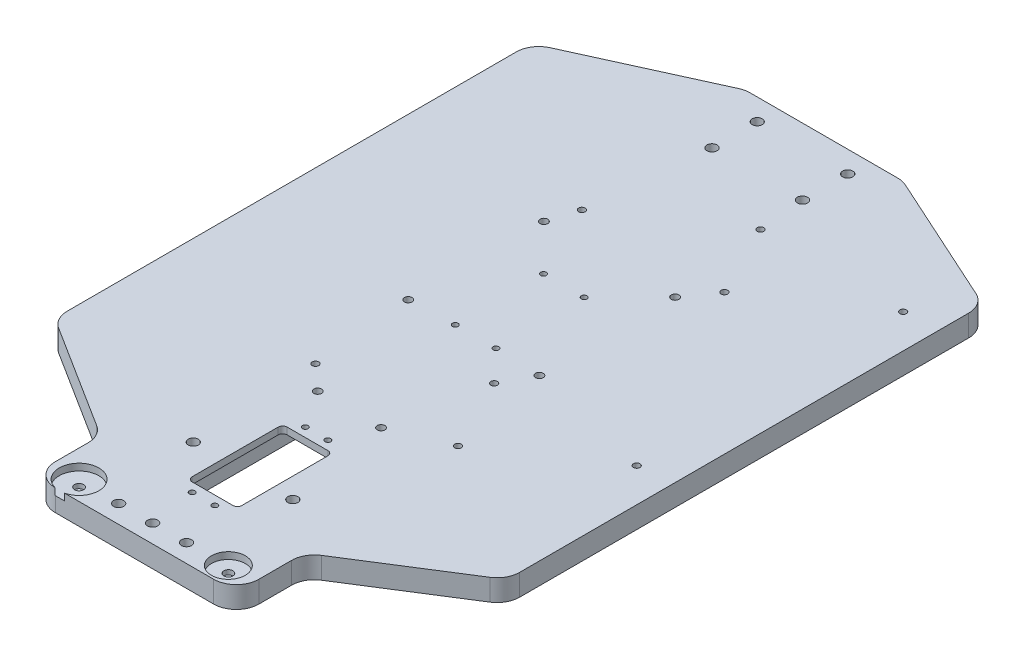
SolidWorks part; units mm, degrees
ref_plane "Front Plane" through (0, 0, 0) normal (0, 0, 1) x (1, 0, 0)
ref_plane "Top Plane" through (0, 0, 0) normal (0, 1, 0) x (1, 0, 0)
ref_plane "Right Plane" through (0, 0, 0) normal (1, 0, 0) x (0, 0, -1)
sketch "Sketch2" plane through (0, 0, 0) normal (0, 1, 0) x (1, 0, 0)
  line L1 (-100, -85.2266) -> (-45, -120)
  line L2 (-45, -120) -> (-45, -150)
  line L3 (-45, -150) -> (0, -150)
  line L4 (0, -150) -> (0, 0)
  line L5 (0, 0) -> (0, 154.8)
  line L6 (0, 154.8) -> (-34.8371, 154.8)
  line L10 (-34.8371, 154.8) -> (-100, 125.1947)
  line L11 (-100, 125.1947) -> (-100, -85.2266)
  dimension "D1" = 304.8
  dimension "D2" = 150
  dimension "D3" = 45
  dimension "D4" = 30
  dimension "D5" = 100
extrude "Chassis Base Shape" add sketch "Sketch2" along normal blind 9.525
hole_wizard "M4 Clearance Hole1" positions "Sketch5" profile "Sketch6" hole size "M4" standard "ANSI Metric" end condition through all
sketch "Sketch5" plane through (0, 0, 0) normal (0, -1, 0) x (-1, 0, 0)
  line L0 (0, -150) -> (0, 154.8) construction
  line L1 (45, -150) -> (0, -150) construction
  point P0 (15, -142)
  point P2 (0, -142)
  point P9 (22, -102)
  dimension "D1" = 15
  dimension "D2" = 8
  dimension "D3" = 22
  dimension "D4" = 40
sketch "Sketch6" plane through (-15, 0, 142) normal (1, 0, 0) x (0, 0, -1)
  line L0 (0, 0) -> (0, 9.525)
  line L1 (0, 9.525) -> (2.25, 9.525)
  line L2 (2.25, 9.525) -> (2.25, 0)
  line L5 (2.25, 0) -> (0, 0)
  line L11 (0, -6.35) -> (0, 107.95) construction
  dimension "Thru Hole Dia." = 4.5
  dimension "Thru Hole Depth" = 9.525
hole_wizard "M4 Clearance Hole2" positions "Sketch11" profile "Sketch12" hole size "M4" standard "ANSI Metric" end condition through all
sketch "Sketch11" plane through (0, 0, 0) normal (0, -1, 0) x (-1, 0, 0)
  line L0 (0, 154.8) -> (34.8371, 154.8) construction
  point P0 (20, 125.3)
  point P2 (20, 145.3)
  dimension "D1" = 20
  dimension "D2" = 9.5
  dimension "D3" = 20
sketch "Sketch12" plane through (-20, 0, -125.3) normal (1, 0, 0) x (0, 0, -1)
  line L0 (0, 0) -> (0, 9.525)
  line L1 (0, 9.525) -> (2.25, 9.525)
  line L2 (2.25, 9.525) -> (2.25, 0)
  line L5 (2.25, 0) -> (0, 0)
  line L11 (0, -6.35) -> (0, 107.95) construction
  dimension "Thru Hole Dia." = 4.5
  dimension "Thru Hole Depth" = 9.525
mirror "Chassis Base Mirror" of "M4 Clearance Hole2", "Chassis Base Shape", "M4 Clearance Hole1"
sketch "Sketch29" plane through (0, 0, 0) normal (0, -1, 0) x (1, 0, 0)
  line L8 (10, 117.5) -> (-6, 117.5)
  line L9 (12, 77.5) -> (12, 115.5)
  line L10 (-6, 75.5) -> (10, 75.5)
  line L11 (-8, 115.5) -> (-8, 77.5)
  arc A8 (12, 115.5) -> (10, 117.5) centre (10, 115.5) ccw
  arc A9 (10, 75.5) -> (12, 77.5) centre (10, 77.5) ccw
  arc A10 (-8, 77.5) -> (-6, 75.5) centre (-6, 77.5) ccw
  arc A11 (-6, 117.5) -> (-8, 115.5) centre (-6, 115.5) ccw
extrude "Cut-Extrude1" [suppressed] cut sketch "Sketch29" against normal through all
fillet "Fillet1" radius 10 10 edges at (-45, 4.7625, 150) (-45, 4.7625, 120) (-100, 4.7625, 85.2266) (-100, 4.7625, -125.1947) (-34.8371, 4.7625, -154.8) (34.8371, 4.7625, -154.8) (100, 4.7625, -125.1947) (100, 4.7625, 85.2266) (45, 4.7625, 120) (45, 4.7625, 150)
sketch "Sketch7" plane through (0, 0, 0) normal (0, -1, 0) x (-1, 0, 0)
  line L0 (-2, -96.5) -> (-2, -105) construction
  line L1 (-12, -126) -> (8, -126)
  line L2 (-14, -124) -> (-14, -69)
  line L3 (-12, -67) -> (8, -67)
  line L4 (10, -124) -> (10, -69)
  line L5 (-14, -126) -> (10, -67) construction
  line L6 (-14, -67) -> (10, -126) construction
  arc A0 (-12, -126) -> (-14, -124) centre (-12, -124) cw
  arc A1 (8, -126) -> (10, -124) centre (8, -124) ccw
  arc A2 (8, -67) -> (10, -69) centre (8, -69) cw
  arc A3 (-14, -69) -> (-12, -67) centre (-12, -69) cw
  circle A4 centre (0, -142) radius 2.25 construction
  circle A8 centre (15, -142) radius 2.25 construction
  point P0 (-2, -96.5)
  dimension "D1" = 2
  dimension "D2" = 24
  dimension "D3" = 59
  dimension "D4" = 8.5
  dimension "D5" = 17
  dimension "D6" = 37
extrude "Servo Recess" cut sketch "Sketch7" against normal offset from surface (6.525 mm away) 3 up to face at (15, 9.525, 139.75)
sketch "Sketch8" plane through (0, 6.525, 0) normal (0, -1, 0) x (1, 0, 0)
  line L2 (-7, 117.5) -> (11, 117.5)
  line L3 (-9, 115.5) -> (-9, 77.5)
  line L4 (-7, 75.5) -> (11, 75.5)
  line L5 (13, 115.5) -> (13, 77.5)
  line L6 (-8, 67) -> (12, 67) construction
  line L11 (14, 69) -> (14, 124) construction
  line L12 (-10, 124) -> (-10, 69) construction
  arc A0 (11, 117.5) -> (13, 115.5) centre (11, 115.5) cw
  arc A1 (-7, 117.5) -> (-9, 115.5) centre (-7, 115.5) ccw
  arc A2 (-9, 77.5) -> (-7, 75.5) centre (-7, 77.5) ccw
  arc A3 (11, 75.5) -> (13, 77.5) centre (11, 77.5) ccw
  dimension "D2" = 2
  dimension "D1" = 1
  dimension "D3" = 8.5
  dimension "D4" = 1
  dimension "D6" = 42
extrude "Servo Cutout" cut sketch "Sketch8" against normal through all
hole_wizard "M3x0.5 Servo" positions "Sketch9" profile "Sketch10" tap size "M3x0.5" standard "ANSI Metric" end condition through all
sketch "Sketch9" plane through (0, 6.525, 0) normal (0, -1, 0) x (-1, 0, 0)
  line L8 (7, -75.5) -> (-11, -75.5) construction
  line L9 (10, -124) -> (10, -69) construction
  point P0 (3, -71.5)
  point P2 (-7, -71.5)
  point P4 (3, -121.5)
  point P6 (-7, -121.5)
  dimension "D1" = 10
  dimension "D2" = 4
  dimension "D3" = 50
  dimension "D4" = 7
sketch "Sketch10" plane through (-3, 6.525, 71.5) normal (1, 0, 0) x (0, 0, -1)
  line L0 (0, 0) -> (0, 3)
  line L1 (0, 3) -> (1.25, 3)
  line L2 (1.25, 3) -> (1.25, 0)
  line L5 (1.25, 0) -> (0, 0)
  line L11 (0, -6.35) -> (0, 107.95) construction
  dimension "Thread Major Dia." = 2.5
  dimension "Thru Tap Drill Depth" = 3
hole_wizard "M2.5 Clearance ESC" positions "Sketch18" profile "Sketch19" hole size "M2.5" standard "ANSI Metric"
sketch "Sketch18" plane through (0, 0, 0) normal (0, -1, 0) x (-1, 0, 0)
  line L4 (25, -45) -> (25, 72.8) construction
  line L6 (-85, -13) -> (-85, 104.8) construction
  line L8 (100, 118.7543) -> (100, -79.718) construction
  line L9 (-100, 118.7543) -> (-100, -79.718) construction
  line L30 (100, 104.8) -> (-100, 104.8) construction
  line L31 (-32.672, 154.8) -> (32.672, 154.8) construction
  line L32 (100, -45) -> (-100, -45) construction
  line L34 (35, -150) -> (-35, -150) construction
  line L35 (25, -13) -> (-85, -13) construction
  line L37 (-22, -45) -> (-22, 104.8) construction
  line L39 (-38, -45) -> (-38, 104.8) construction
  line L41 (25, 72.8) -> (-85, 72.8) construction
  point P14 (25, 72.8)
  point P17 (-85, -13)
  point P151 (25, -45)
  point P152 (-22, -13)
  point P156 (-22, 104.8)
  point P223 (-38, -45)
  point P491 (-85, 104.8)
  point P492 (-38, 72.8)
  dimension "D1" = 75
  dimension "D2" = 15
  dimension "D3" = 47
  dimension "D4" = 32
  dimension "D5" = 47
  dimension "D6" = 32
  dimension "D11" = 50
  dimension "D12" = 105
sketch "Sketch19" plane through (-25, 0, -72.8) normal (1, 0, 0) x (0, 0, -1)
  line L0 (0, 0) -> (0, 10.3952)
  line L1 (0, 10.3952) -> (1.45, 9.524)
  line L2 (1.45, 9.524) -> (1.45, 0)
  line L5 (1.45, 0) -> (0, 0)
  line L10 (0, 10.3952) -> (-1.45, 9.524) construction
  line L11 (0, -6.35) -> (0, 107.95) construction
  dimension "Hole Dia." = 2.9
  dimension "Hole Depth" = 9.524
  dimension "Drill Angle" = 118
hole_wizard "Tap Drill for Reciever M3x0.5 Tap1" [suppressed] positions "Sketch20" profile "Sketch21" hole size "M3x0.5" standard "ANSI Metric"
sketch "Sketch20" plane through (0, 0, 0) normal (0, -1, 0) x (-1, 0, 0)
  line L1 (8, -67) -> (-12, -67) construction
  line L2 (100, 118.7543) -> (100, -79.718) construction
  point P0 (-40, 18)
  point P2 (-2, 18)
  dimension "D1" = 38
  dimension "D2" = 140
  dimension "D3" = 85
sketch "Sketch21" plane through (40, 0, -18) normal (1, 0, 0) x (0, 0, -1)
  line L0 (0, 0) -> (0, 5.7511)
  line L1 (0, 5.7511) -> (1.25, 5)
  line L2 (1.25, 5) -> (1.25, 0)
  line L5 (1.25, 0) -> (0, 0)
  line L10 (0, 5.7511) -> (-1.25, 5) construction
  line L11 (0, -6.35) -> (0, 107.95) construction
  dimension "Hole Dia." = 2.5
  dimension "Hole Depth" = 5
  dimension "Drill Angle" = 118
hole_wizard "M2.5x0.45 Tap for RPi" positions "Sketch25" profile "Sketch26" hole size "M2.5x0.45" standard "ANSI Metric"
sketch "Sketch25" plane through (0, 0, 0) normal (0, -1, 0) x (-1, 0, 0)
  line L1 (100, 118.7543) -> (100, -79.718) construction
  line L2 (-32.672, 154.8) -> (32.672, 154.8) construction
  point P0 (90, -13.2)
  point P2 (41, -13.2)
  point P4 (41, 44.8)
  point P6 (90, 44.8)
  dimension "D1" = 58
  dimension "D2" = 49
  dimension "D3" = 10
  dimension "D4" = 110
sketch "Sketch26" plane through (-90, 0, 13.2) normal (1, 0, 0) x (0, 0, -1)
  line L0 (0, 0) -> (0, 5.6159)
  line L1 (0, 5.6159) -> (1.025, 5)
  line L2 (1.025, 5) -> (1.025, 0)
  line L5 (1.025, 0) -> (0, 0)
  line L10 (0, 5.6159) -> (-1.025, 5) construction
  line L11 (0, -6.35) -> (0, 107.95) construction
  dimension "Hole Dia." = 2.05
  dimension "Hole Depth" = 5
  dimension "Drill Angle" = 118
sketch "Sketch27" plane through (0, 9.525, 0) normal (0, 1, 0) x (1, 0, 0)
  line L0 (0, -150) -> (0, -92.8191) construction
  line L1 (-35, -150) -> (35, -150) construction
  circle A0 centre (-33, -141.5) radius 8.75
  circle A1 centre (33, -141.5) radius 7.5
  dimension "D1" = 17.5
  dimension "D2" = 15
  dimension "D3" = 66
  dimension "D4" = 33
  dimension "D5" = 8.5
extrude "Bellcrank Positions" cut sketch "Sketch27" against normal blind 3
sketch "Sketch28" plane through (0, 6.525, 0) normal (0, 1, 0) x (1, 0, 0)
  circle A0 centre (-33, -141.5) radius 2
  circle A1 centre (33, -141.5) radius 2
  circle A2 centre (33, -141.5) radius 7.5 construction
  arc A3 (-30.9233, -150) -> (-35.0779, -149.9997) centre (-33, -141.5) ccw construction
  dimension "D1" = 4
  dimension "D2" = 4
extrude "Dowel Screw Cap Slots" cut sketch "Sketch28" against normal blind 2
hole_wizard "Battery Holes" positions "Sketch30" profile "Sketch31" hole size "M3" standard "ANSI Metric" end condition through all
sketch "Sketch30" plane through (0, 9.525, 0) normal (0, 1, 0) x (1, 0, 0)
  line L3 (0, 154.8) -> (0, -171.1531) construction
  line L4 (32.672, 154.8) -> (-32.672, 154.8) construction
  line L6 (-30.9233, -150) -> (35, -150) construction
  point P0 (-14, -55)
  point P6 (-29, 0)
  point P8 (-29, 60)
  point P30 (29, 60)
  point P31 (29, 0)
  point P32 (14, -55)
  dimension "D1" = 28
  dimension "D2" = 58
  dimension "D3" = 95
  dimension "D4" = 55
  dimension "D5" = 115
sketch "Sketch31" plane through (-14, 9.525, 55) normal (1, 0, 0) x (0, 0, 1)
  line L0 (0, 0) -> (0, 9.525)
  line L1 (0, 9.525) -> (1.7, 9.525)
  line L2 (1.7, 9.525) -> (1.7, 0)
  line L5 (1.7, 0) -> (0, 0)
  line L11 (0, -6.35) -> (0, 107.95) construction
  dimension "Thru Hole Dia." = 3.4
  dimension "Thru Hole Depth" = 9.525
hole_wizard "Tap Drill for M3x0.5 Tap1" positions "Sketch32" profile "Sketch33" hole size "M3x0.5" standard "ANSI Metric" end condition up to next
sketch "Sketch32" plane through (0, 0, 0) normal (0, -1, 0) x (-1, 0, 0)
  line L0 (0, -150) -> (0, 154.8) construction
  line L1 (35, -150) -> (-35, -150) construction
  line L2 (-32.672, 154.8) -> (32.672, 154.8) construction
  point P0 (9, 0.8)
  point P2 (-9, 0.8)
  point P4 (9, 39.8)
  point P6 (-9, 39.8)
  dimension "D1" = 9
  dimension "D2" = 18
  dimension "D3" = 18
  dimension "D4" = 39
  dimension "D5" = 115
sketch "Sketch33" plane through (-9, 0, -0.8) normal (1, 0, 0) x (0, 0, -1)
  line L0 (0, 0) -> (0, 9.525)
  line L1 (0, 9.525) -> (1.25, 9.525)
  line L2 (1.25, 9.525) -> (1.25, 0)
  line L5 (1.25, 0) -> (0, 0)
  line L11 (0, -6.35) -> (0, 107.95) construction
  dimension "Thru Hole Dia." = 2.5
  dimension "Thru Hole Depth" = 9.525
